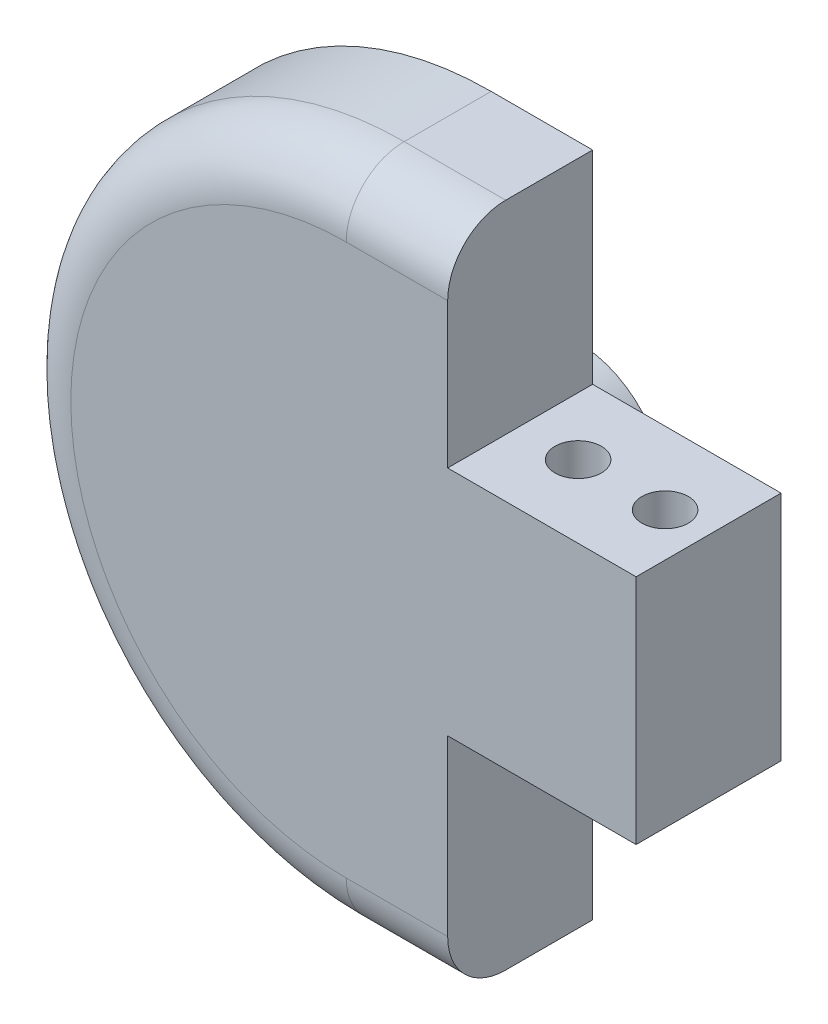
SolidWorks part; units mm, degrees
ref_plane "Front" through (0, 0, 0) normal (0, 0, 1) x (1, 0, 0)
ref_plane "Top" through (0, 0, 0) normal (0, 1, 0) x (1, 0, 0)
ref_plane "Right" through (0, 0, 0) normal (1, 0, 0) x (0, 0, -1)
sketch "Sketch1" plane through (0, 0, 0) normal (0, 0, 1) x (1, 0, 0)
  line L0 (-11, 0) -> (-1, 0) construction
  line L1 (-1, 0) -> (9, 0) construction
  line L2 (3.5, 12) -> (3.5, 5)
  line L3 (3.5, 5) -> (10, 5)
  line L5 (10, -3) -> (3.5, -3)
  line L6 (10, 5) -> (10, -3)
  line L7 (0, 12) -> (3.5, 12)
  line L8 (0, -11) -> (3.5, -11)
  line L9 (3.5, -3) -> (3.5, -11)
  arc A1 (0, 12) -> (0, -11) centre (0, 0.5) ccw
extrude "Boss-Extrude1" add sketch "Sketch1" along normal blind 5
sketch "Sketch2" plane through (0, 0, 0) normal (0, 1, 0) x (1, 0, 0)
  line L0 (10, -2.5) -> (8.5, -2.5) construction
  line L2 (8.5, -2.5) -> (5.5, -2.5) construction
  circle A0 centre (8.5, -2.5) radius 0.8
  circle A1 centre (5.5, -2.5) radius 0.8
extrude "Cut-Extrude1" cut sketch "Sketch2" against normal through all from offset 11
sketch "Sketch4" plane through (0, 0, 0) normal (0, 0, 1) x (1, 0, 0)
  circle A0 centre (0, 0) radius 3
extrude "Boss-Extrude2" add sketch "Sketch4" against normal blind 3
fillet "Fillet1" radius 2 3 edges at (1.75, 12, 5) (1.75, -11, 5) (-11.5, 0.5, 5)
